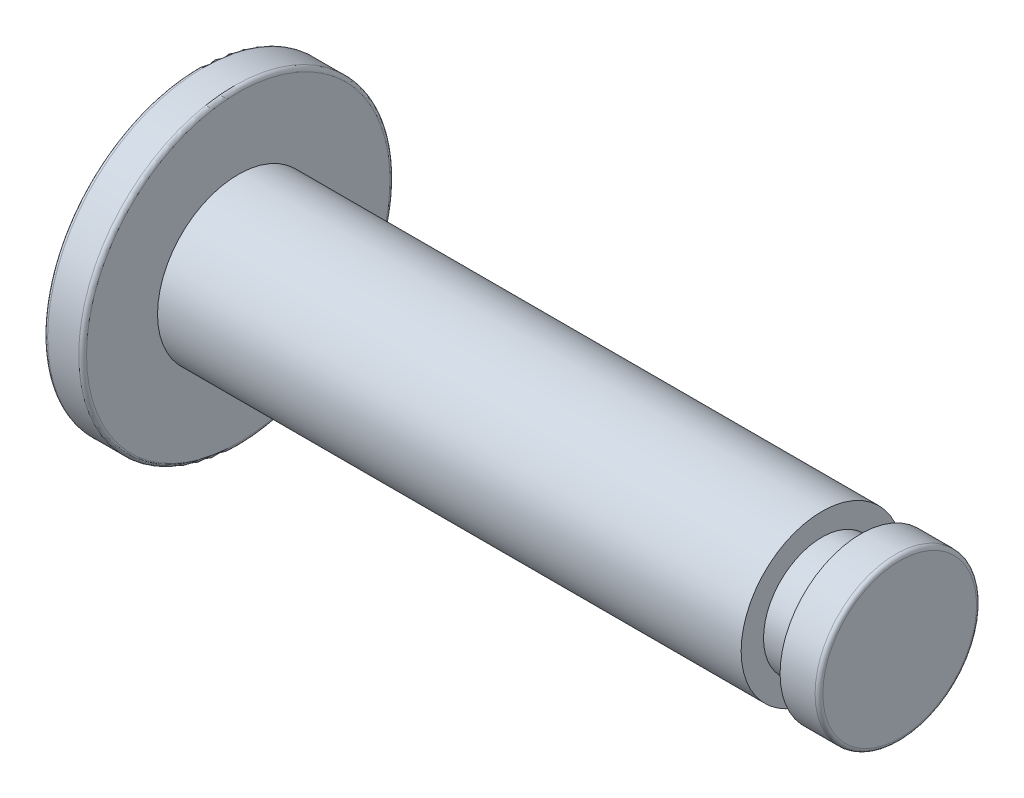
SolidWorks part; units mm, degrees
material "AISI 304"
ref_plane "Front Plane" through (0, 0, 0) normal (0, 0, 1) x (1, 0, 0)
ref_plane "Top Plane" through (0, 0, 0) normal (0, 1, 0) x (1, 0, 0)
ref_plane "Right Plane" through (0, 0, 0) normal (1, 0, 0) x (0, 0, -1)
sketch "Sketch1" plane through (0, 0, 0) normal (0, 0, 1) x (1, 0, 0)
  line L0 (0, 0) -> (0, 4)
  line L1 (0, 4) -> (1, 4)
  line L2 (1, 4) -> (1, 2.075)
  line L3 (1, 2.075) -> (16, 2.075)
  line L4 (16, 2.075) -> (16, 1.5)
  line L5 (16, 1.5) -> (17, 1.5)
  line L6 (17, 1.5) -> (17, 2.075)
  line L7 (17, 2.075) -> (18, 2.075)
  line L8 (18, 2.075) -> (18, 0)
  line L9 (18, 0) -> (0, 0)
  line L10 (-1.6197, 0) -> (7.7083, 0) construction
  dimension "D1" = 4.15
  dimension "D2" = 8
  dimension "D3" = 1
  dimension "D4" = 1
  dimension "D5" = 1
  dimension "Length" = 15
  dimension "D7" = 3
revolve "Revolve1" add sketch "Sketch1" angle 360 about L10
fillet "Fillet1" radius 0.1 3 edges at (18, 0, 2.075) (0, 0, 4) (1, 0, 4)
